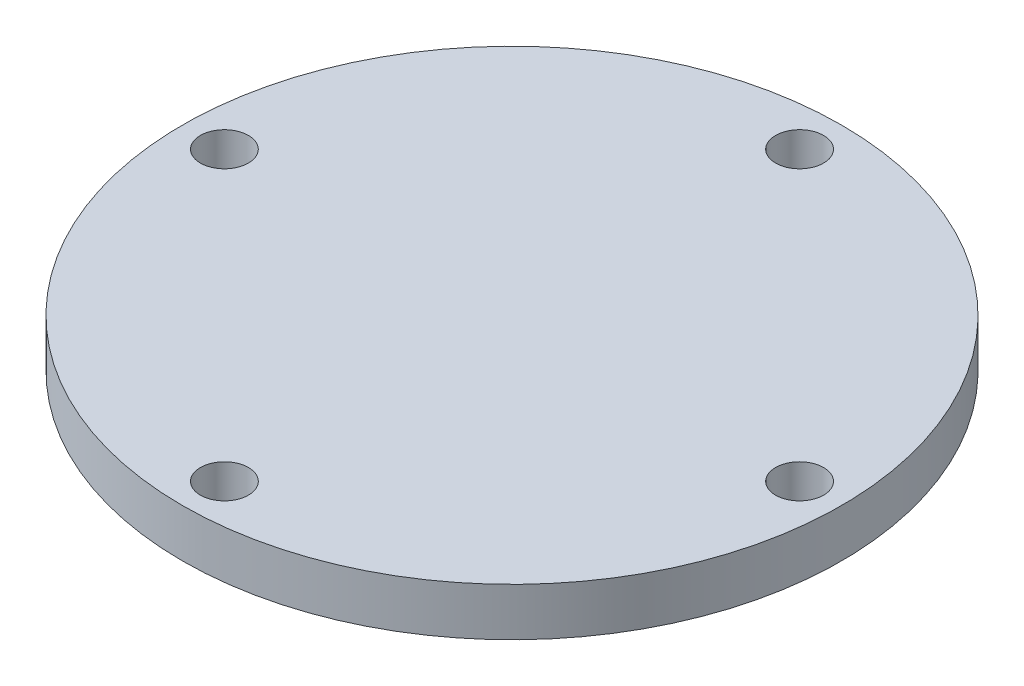
SolidWorks part; units mm, degrees
ref_plane "Front Plane" through (0, 0, 0) normal (0, 0, 1) x (1, 0, 0)
ref_plane "Top Plane" through (0, 0, 0) normal (0, 1, 0) x (1, 0, 0)
ref_plane "Right Plane" through (0, 0, 0) normal (1, 0, 0) x (0, 0, -1)
sketch "Sketch2" plane through (0, 0, 0) normal (0, 1, 0) x (1, 0, 0)
  circle A0 centre (0, 0) radius 27.469
  dimension "D1" = 54.938
extrude "Boss-Extrude1" add sketch "Sketch2" along normal blind 4
sketch "Sketch3" plane through (0, 4, 0) normal (0, 1, 0) x (1, 0, 0)
  circle A1 centre (-23.971, 0) radius 2
  circle A2 centre (0, 23.971) radius 2
  circle A3 centre (23.971, 0) radius 2
  circle A4 centre (0, -23.971) radius 2
  point P14 (0, 0)
  dimension "D2" = 4
  dimension "D1" = 4
extrude "Cut-Extrude1" cut sketch "Sketch3" against normal through all
